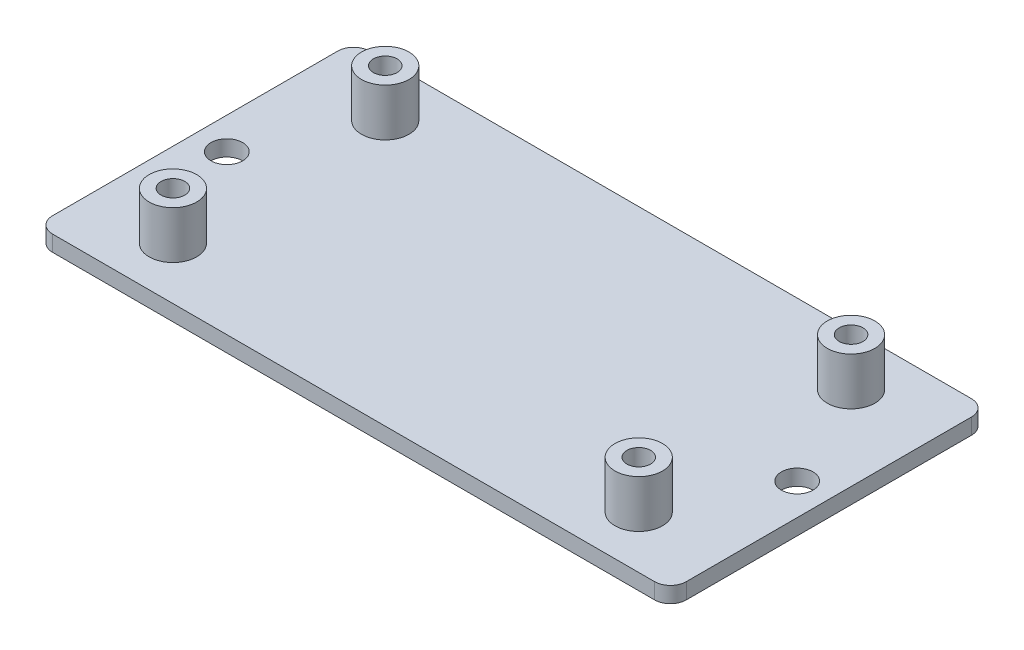
SolidWorks part; units mm, degrees
material "ABS"
ref_plane "Спереди" through (0, 0, 0) normal (0, 0, 1) x (1, 0, 0)
ref_plane "Сверху" through (0, 0, 0) normal (0, 1, 0) x (1, 0, 0)
ref_plane "Справа" through (0, 0, 0) normal (1, 0, 0) x (0, 0, -1)
sketch "Эскиз1" plane through (0, 0, 0) normal (0, 1, 0) x (1, 0, 0)
  line L1 (0, 0) -> (80, 0)
  line L2 (0, 0) -> (0, -40)
  line L3 (0, -40) -> (80, -40)
  line L4 (80, 0) -> (80, -40)
  dimension "D1" = 40
  dimension "D2" = 80
extrude "Бобышка-Вытянуть1" add sketch "Эскиз1" along normal blind 2
sketch "Эскиз2" plane through (0, 2, 0) normal (0, 1, 0) x (1, 0, 0)
  line L0 (0, 0) -> (0, -40) construction
  line L1 (80, 0) -> (0, 0) construction
  line L2 (0, -40) -> (80, -40) construction
  line L3 (80, -40) -> (80, 0) construction
  circle A0 centre (10.6, -6.6) radius 3
  circle A1 centre (10.6, -33.4) radius 3
  circle A2 centre (69.4, -6.6) radius 3
  circle A3 centre (69.4, -33.4) radius 3
  dimension "D1" = 10.6
  dimension "D2" = 6.6
  dimension "D3" = 10.6
  dimension "D4" = 6.6
  dimension "D5" = 6.6
  dimension "D6" = 10.6
  dimension "D7" = 10.6
  dimension "D8" = 6.6
  dimension "D9" = 6
  dimension "D10" = 6
  dimension "D11" = 6
  dimension "D12" = 6
extrude "Бобышка-Вытянуть2" add sketch "Эскиз2" along normal blind 6
sketch "Эскиз3" plane through (0, 8, 0) normal (0, 1, 0) x (1, 0, 0)
  circle A0 centre (10.6, -6.6) radius 1.5
  circle A1 centre (10.6, -33.4) radius 1.5
  circle A2 centre (69.4, -6.6) radius 1.5
  circle A3 centre (69.4, -33.4) radius 1.5
  dimension "D1" = 3
  dimension "D2" = 3
  dimension "D3" = 3
  dimension "D4" = 3
extrude "Вырез-Вытянуть1" cut sketch "Эскиз3" against normal through all both and the other way through all
sketch "Эскиз4" plane through (0, 2, 0) normal (0, 1, 0) x (1, 0, 0)
  line L0 (0, -20) -> (80, -20) construction
  line L1 (0, 0) -> (0, -40) construction
  line L2 (80, -40) -> (80, 0) construction
  circle A0 centre (4, -20) radius 2
  circle A1 centre (76, -20) radius 2
  dimension "D1" = 4
  dimension "D2" = 4
  dimension "D3" = 4
  dimension "D4" = 4
extrude "Вырез-Вытянуть2" cut sketch "Эскиз4" against normal through all both and the other way through all
fillet "Скругление1" radius 2 1 edges at (0, 1, 0)
fillet "Скругление2" radius 2 1 edges at (0, 1, 40)
fillet "Скругление3" radius 2 1 edges at (80, 1, 40)
fillet "Скругление4" radius 2 1 edges at (80, 1, 0)
